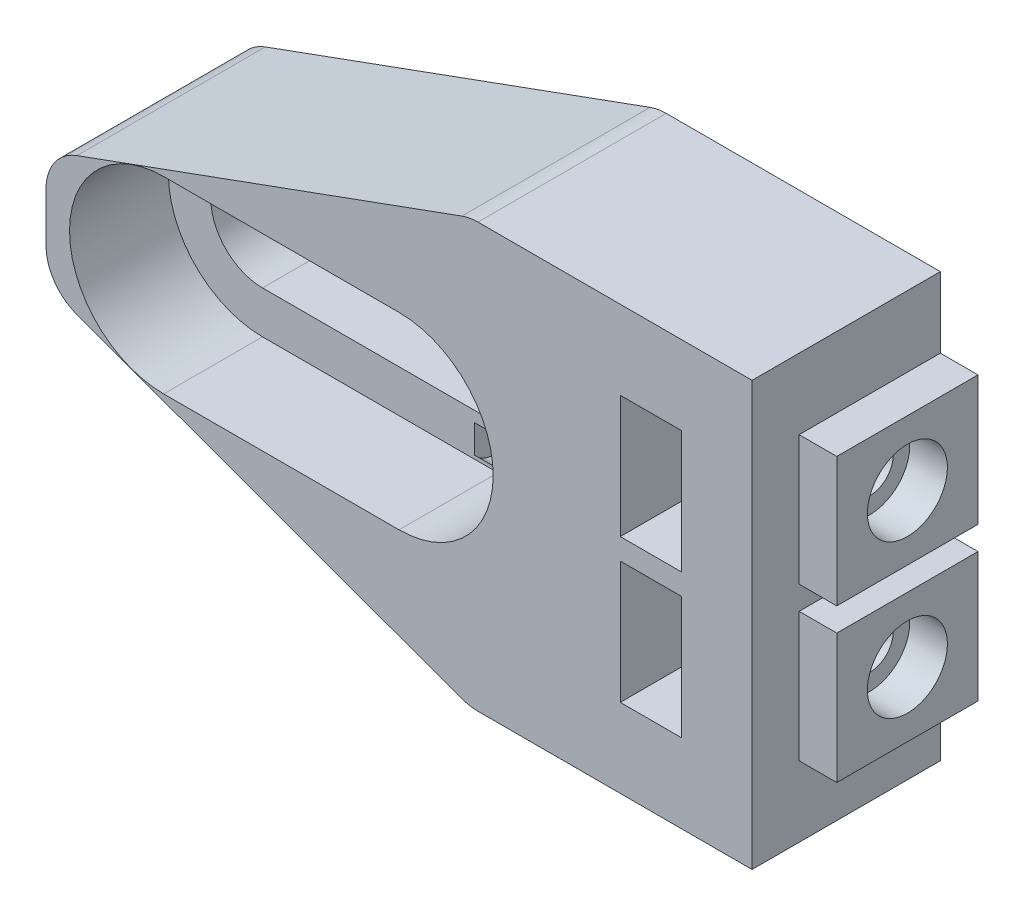
SolidWorks part; units mm, degrees
ref_plane "Plan de face" through (0, 0, 0) normal (0, 0, 1) x (1, 0, 0)
ref_plane "Plan de dessus" through (0, 0, 0) normal (0, 1, 0) x (1, 0, 0)
ref_plane "Plan de droite" through (0, 0, 0) normal (1, 0, 0) x (0, 0, -1)
sketch "Esquisse1" plane through (0, 0, 0) normal (0, 0, 1) x (1, 0, 0)
  line L1 (-8, 9) -> (22, 9)
  line L2 (-8, 9) -> (-8, -9)
  line L3 (-8, -9) -> (22, -9)
  line L4 (22, 9) -> (22, -9)
  dimension "D1" = 18
  dimension "D2" = 30
  dimension "D3" = 9
  dimension "D4" = 8
extrude "Boss.-Extru.1" add sketch "Esquisse1" along normal blind 8
sketch "Esquisse2" plane through (0, 0, 8) normal (0, 0, 1) x (1, 0, 0)
  line L0 (-8, 9) -> (-8, -9) construction
  line L1 (22, 9) -> (-8, 9) construction
  line L2 (-3, 0) -> (7, 0) construction
  line L3 (-3, 2.2) -> (7, 2.2)
  line L4 (-3, -2.2) -> (7, -2.2)
  arc A1 (-3, 2.2) -> (-3, -2.2) centre (-3, 0) ccw
  arc A2 (7, -2.2) -> (7, 2.2) centre (7, 0) ccw
  point P2 (2, 0)
  dimension "D1" = 9
  dimension "D4" = 2.2
  dimension "D2" = 5
  dimension "D3" = 9
  dimension "D5" = 10
extrude "Enlèv. mat.-Extru.1" cut sketch "Esquisse2" against normal through all
sketch "Esquisse3" plane through (0, 0, 8) normal (0, 0, 1) x (1, 0, 0)
  line L0 (-3, 0) -> (7, 0) construction
  line L1 (-3, 4) -> (7, 4)
  line L2 (-3, -4) -> (7, -4)
  arc A2 (-3, 4) -> (-3, -4) centre (-3, 0) ccw
  arc A3 (7, -4) -> (7, 4) centre (7, 0) ccw
  point P6 (2, 0)
  dimension "D2" = 4
extrude "Enlèv. mat.-Extru.2" cut sketch "Esquisse3" against normal blind 4.2
chamfer "Chanfrein1" distance 18 angle 20 2 edges at (-8, -9, 4) (-8, 9, 4)
fillet "Congé1" radius 2 4 edges at (10, -9, 4) (10, 9, 4) (-8, -2.4485, 4) (-8, 2.4485, 4)
sketch "Esquisse4" plane through (0, 0, 0) normal (0, 0, -1) x (-1, 0, 0)
  line L0 (-22, -9) -> (-22, 9) construction
  line L1 (-19, -5.65) -> (-16.4, -5.65)
  line L2 (-19, -5.65) -> (-19, -0.45)
  line L3 (-19, -0.45) -> (-16.4, -0.45)
  line L4 (-16.4, -5.65) -> (-16.4, -0.45)
  line L5 (-19, 0.45) -> (-16.4, 0.45)
  line L6 (-19, 0.45) -> (-19, 5.65)
  line L7 (-19, 5.65) -> (-16.4, 5.65)
  line L8 (-16.4, 0.45) -> (-16.4, 5.65)
  arc A0 (-7, 2.2) -> (-7, -2.2) centre (-7, 0) ccw construction
  point P10 (-9.2, 0)
  dimension "D1" = 5.2
  dimension "D2" = 5.2
  dimension "D3" = 0.9
  dimension "D4" = 3
  dimension "D5" = 0.45
  dimension "D6" = 2.6
  dimension "D7" = 2.6
  dimension "D8" = 3
extrude "Enlèv. mat.-Extru.3" cut sketch "Esquisse4" against normal through all
sketch "Esquisse5" plane through (22, 0, 0) normal (1, 0, 0) x (0, 0, -1)
  line L0 (0, -9) -> (0, 9) construction
  line L2 (0, -2.2) -> (0, 2.2) construction
  circle A0 centre (-3, 3.25) radius 1
  circle A1 centre (-3, -3.25) radius 1
  point P6 (0, 0)
  dimension "D1" = 2
  dimension "D2" = 2
  dimension "D5" = 3.25
  dimension "D3" = 6.5
  dimension "D4" = 3
  dimension "D6" = 3
extrude "Enlèv. mat.-Extru.4" cut sketch "Esquisse5" against normal blind 16
sketch "Esquisse6" plane through (22, 0, 0) normal (1, 0, 0) x (0, 0, -1)
  line L0 (0, -9) -> (0, 9) construction
  line L1 (0, -6) -> (-6, -6)
  line L2 (0, -6) -> (0, -0.5)
  line L3 (0, -0.5) -> (-6, -0.5)
  line L4 (-6, -6) -> (-6, -0.5)
  line L6 (0, 0.5) -> (-6, 0.5)
  line L7 (0, 0.5) -> (0, 6)
  line L8 (0, 6) -> (-6, 6)
  line L9 (-6, 0.5) -> (-6, 6)
  circle A0 centre (-3, -3.25) radius 1.7
  circle A1 centre (-3, 3.25) radius 1.7
  dimension "D1" = 5.5
  dimension "D2" = 6
  dimension "D3" = 2.75
  dimension "D4" = 5.5
  dimension "D5" = 2.75
  dimension "D6" = 6
extrude "Boss.-Extru.2" add sketch "Esquisse6" along normal blind 1.6
